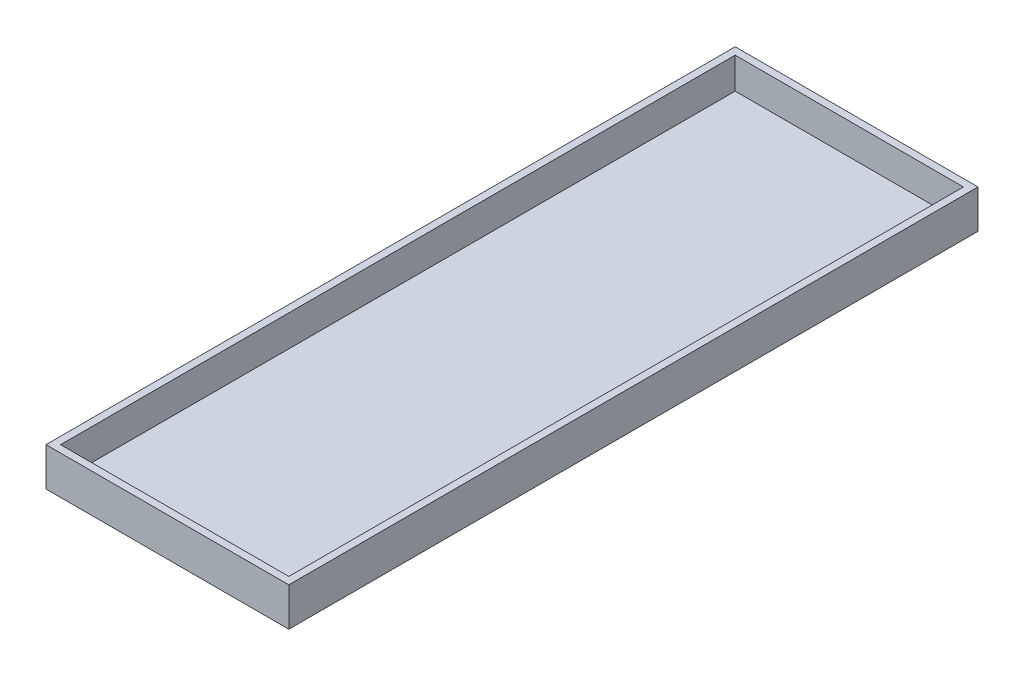
SolidWorks part; units mm, degrees
ref_plane "Front Plane" through (0, 0, 0) normal (0, 0, 1) x (1, 0, 0)
ref_plane "Top Plane" through (0, 0, 0) normal (0, 1, 0) x (1, 0, 0)
ref_plane "Right Plane" through (0, 0, 0) normal (1, 0, 0) x (0, 0, -1)
sketch "Sketch1" plane through (0, 0, 0) normal (0, 1, 0) x (1, 0, 0)
  line L1 (0, 0) -> (60, 0)
  line L2 (0, 0) -> (0, 170.3)
  line L3 (0, 170.3) -> (60, 170.3)
  line L4 (60, 0) -> (60, 170.3)
  dimension "D1" = 170.3
  dimension "D2" = 60
extrude "Boss-Extrude4" add sketch "Sketch1" along normal blind 9.5 contours L2 L1 L4 L3
shell "Shell1" thickness 1.8
